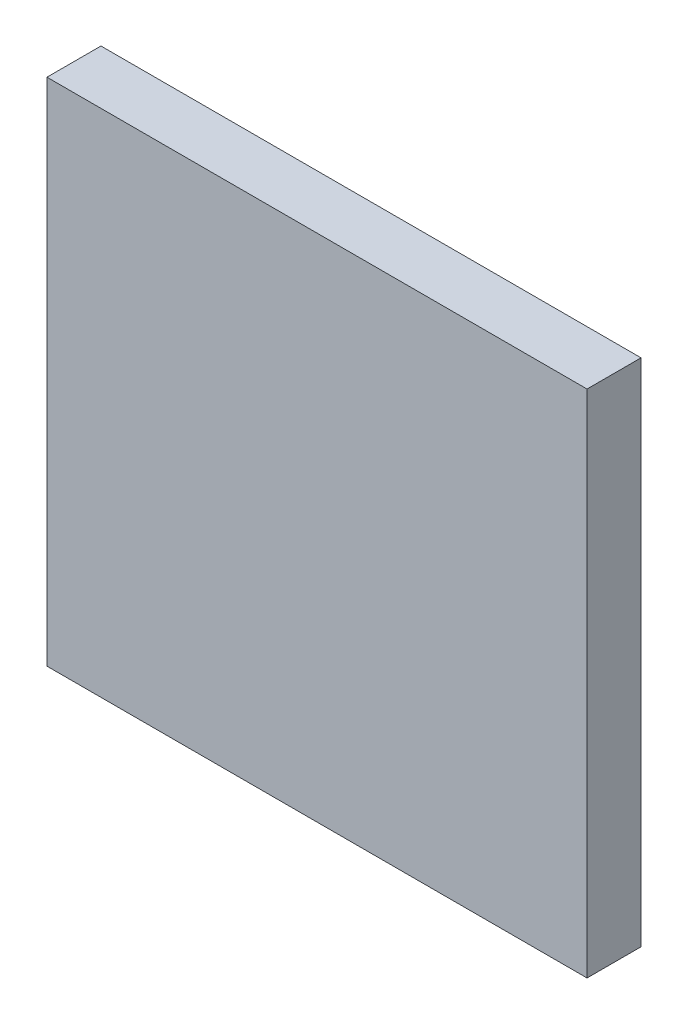
SolidWorks part; units mm, degrees
ref_plane "Спереди" through (0, 0, 0) normal (0, 0, 1) x (1, 0, 0)
ref_plane "Сверху" through (0, 0, 0) normal (0, 1, 0) x (1, 0, 0)
ref_plane "Справа" through (0, 0, 0) normal (1, 0, 0) x (0, 0, -1)
sketch "Эскиз1" plane through (0, 0, 0) normal (0, 0, 1) x (1, 0, 0)
  line L1 (177.7479, -10.1343) -> (-2.2521, -10.1343)
  line L2 (177.7479, -10.1343) -> (177.7479, 159.8657)
  line L3 (177.7479, 159.8657) -> (-2.2521, 159.8657)
  line L4 (-2.2521, -10.1343) -> (-2.2521, 159.8657)
  dimension "D1" = 170
  dimension "D2" = 180
extrude "Бобышка-Вытянуть1" add sketch "Эскиз1" along normal blind 18
